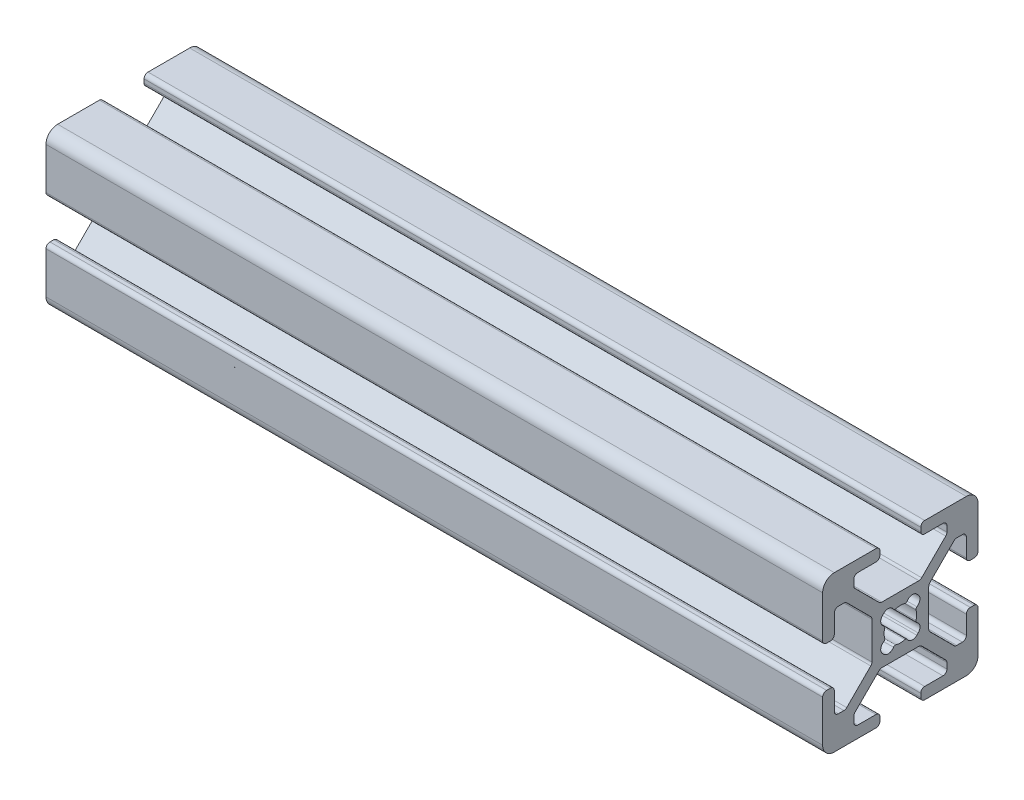
SolidWorks part; units mm, degrees
ref_plane "Front Plane" through (0, 0, 0) normal (0, 0, 1) x (1, 0, 0)
ref_plane "Top Plane" through (0, 0, 0) normal (0, 1, 0) x (1, 0, 0)
ref_plane "Right Plane" through (0, 0, 0) normal (1, 0, 0) x (0, 0, -1)
sketch "Sketch1" plane through (0, 0, 0) normal (0, 0, 1) x (1, 0, 0)
  line L0 (0, 0) -> (100, 0)
  dimension "D1" = 100
other "20_series 20-2020(1)"
ref_plane "Plane1" through (0, 0, 0) normal (1, 0, 0) x (0, 1, 0)
sketch "Sketch11" plane through (0, 0, 0) normal (1, 0, 0) x (0, 1, 0)
  line L0 (9.0094, 2.6289) -> (9.492, 2.6289)
  line L1 (8.5014, 5.4864) -> (8.5014, 3.1369)
  line L2 (10, 8.5014) -> (10, 3.1369)
  line L3 (7.2645, 5.9944) -> (7.9934, 5.9944)
  line L4 (3.1369, 10) -> (8.5014, 10)
  line L5 (3.8074, 2.7477) -> (6.9053, 5.8456)
  line L6 (2.6289, 9.0094) -> (2.6289, 9.492)
  line L7 (3.6586, -2.3885) -> (3.6586, 2.3885)
  line L8 (3.1369, 8.5014) -> (5.4864, 8.5014)
  line L9 (6.9053, -5.8456) -> (3.8074, -2.7477)
  line L10 (5.9944, 7.9934) -> (5.9944, 7.2645)
  line L11 (7.9934, -5.9944) -> (7.2645, -5.9944)
  line L12 (5.8456, 6.9053) -> (2.7477, 3.8074)
  line L13 (8.5014, -3.1369) -> (8.5014, -5.4864)
  line L14 (2.3885, 3.6586) -> (-2.3885, 3.6586)
  line L15 (9.0094, -2.6289) -> (9.492, -2.6289)
  line L16 (-2.7477, 3.8074) -> (-5.8456, 6.9053)
  line L17 (10, -3.1369) -> (10, -8.5014)
  line L18 (-5.9944, 7.2645) -> (-5.9944, 7.9934)
  line L19 (8.5014, -10) -> (3.1369, -10)
  line L20 (-5.4864, 8.5014) -> (-3.1369, 8.5014)
  line L21 (2.6289, -9.0094) -> (2.6289, -9.492)
  line L22 (-2.6289, 9.0094) -> (-2.6289, 9.492)
  line L23 (5.4864, -8.5014) -> (3.1369, -8.5014)
  line L24 (-8.5014, 10) -> (-3.1369, 10)
  line L25 (5.9944, -7.2645) -> (5.9944, -7.9934)
  line L26 (-10, 3.1369) -> (-10, 8.5014)
  line L27 (2.7477, -3.8074) -> (5.8456, -6.9053)
  line L28 (-9.0094, 2.6289) -> (-9.492, 2.6289)
  line L29 (-2.3885, -3.6586) -> (2.3885, -3.6586)
  line L30 (-8.5014, 3.1369) -> (-8.5014, 5.4864)
  line L31 (-5.8456, -6.9053) -> (-2.7477, -3.8074)
  line L32 (-7.9934, 5.9944) -> (-7.2645, 5.9944)
  line L33 (-5.9944, -7.9934) -> (-5.9944, -7.2645)
  line L34 (-6.9053, 5.8456) -> (-3.8074, 2.7477)
  line L35 (-3.1369, -8.5014) -> (-5.4864, -8.5014)
  line L36 (-3.6586, 2.3885) -> (-3.6586, -2.3885)
  line L37 (-2.6289, -9.0094) -> (-2.6289, -9.492)
  line L38 (-3.8074, -2.7477) -> (-6.9053, -5.8456)
  line L39 (-3.1369, -10) -> (-8.5014, -10)
  line L40 (-7.2645, -5.9944) -> (-7.9934, -5.9944)
  line L41 (-10, -8.5014) -> (-10, -3.1369)
  line L42 (-8.5014, -5.4864) -> (-8.5014, -3.1369)
  line L43 (-9.0094, -2.6289) -> (-9.492, -2.6289)
  line L44 (-2.2966, 2.1217) -> (-2.1217, 2.2966)
  line L45 (2.1217, 2.2966) -> (2.2966, 2.1217)
  line L46 (-2.1217, -2.2966) -> (-2.2966, -2.1217)
  line L47 (2.2966, -2.1217) -> (2.1217, -2.2966)
  arc A0 (8.5014, 3.1369) -> (9.0094, 2.6289) centre (9.0094, 3.1369) ccw
  arc A1 (9.492, 2.6289) -> (10, 3.1369) centre (9.492, 3.1369) ccw
  arc A2 (8.5014, 5.4864) -> (7.9934, 5.9944) centre (7.9934, 5.4864) ccw
  arc A3 (10, 8.5014) -> (8.5014, 10) centre (8.5014, 8.5014) ccw
  arc A4 (7.2645, 5.9944) -> (6.9053, 5.8456) centre (7.2645, 5.4864) ccw
  arc A5 (3.1369, 10) -> (2.6289, 9.492) centre (3.1369, 9.492) ccw
  arc A6 (3.8074, 2.7477) -> (3.6586, 2.3885) centre (4.1666, 2.3885) ccw
  arc A7 (2.6289, 9.0094) -> (3.1369, 8.5014) centre (3.1369, 9.0094) ccw
  arc A8 (3.6586, -2.3885) -> (3.8074, -2.7477) centre (4.1666, -2.3885) ccw
  arc A9 (5.9944, 7.9934) -> (5.4864, 8.5014) centre (5.4864, 7.9934) ccw
  arc A10 (6.9053, -5.8456) -> (7.2645, -5.9944) centre (7.2645, -5.4864) ccw
  arc A11 (5.8456, 6.9053) -> (5.9944, 7.2645) centre (5.4864, 7.2645) ccw
  arc A12 (7.9934, -5.9944) -> (8.5014, -5.4864) centre (7.9934, -5.4864) ccw
  arc A13 (2.3885, 3.6586) -> (2.7477, 3.8074) centre (2.3885, 4.1666) ccw
  arc A14 (9.0094, -2.6289) -> (8.5014, -3.1369) centre (9.0094, -3.1369) ccw
  arc A15 (-2.7477, 3.8074) -> (-2.3885, 3.6586) centre (-2.3885, 4.1666) ccw
  arc A16 (10, -3.1369) -> (9.492, -2.6289) centre (9.492, -3.1369) ccw
  arc A17 (-5.9944, 7.2645) -> (-5.8456, 6.9053) centre (-5.4864, 7.2645) ccw
  arc A18 (8.5014, -10) -> (10, -8.5014) centre (8.5014, -8.5014) ccw
  arc A19 (-5.4864, 8.5014) -> (-5.9944, 7.9934) centre (-5.4864, 7.9934) ccw
  arc A20 (2.6289, -9.492) -> (3.1369, -10) centre (3.1369, -9.492) ccw
  arc A21 (-3.1369, 8.5014) -> (-2.6289, 9.0094) centre (-3.1369, 9.0094) ccw
  arc A22 (3.1369, -8.5014) -> (2.6289, -9.0094) centre (3.1369, -9.0094) ccw
  arc A23 (-2.6289, 9.492) -> (-3.1369, 10) centre (-3.1369, 9.492) ccw
  arc A24 (5.4864, -8.5014) -> (5.9944, -7.9934) centre (5.4864, -7.9934) ccw
  arc A25 (-8.5014, 10) -> (-10, 8.5014) centre (-8.5014, 8.5014) ccw
  arc A26 (5.9944, -7.2645) -> (5.8456, -6.9053) centre (5.4864, -7.2645) ccw
  arc A27 (-10, 3.1369) -> (-9.492, 2.6289) centre (-9.492, 3.1369) ccw
  arc A28 (2.7477, -3.8074) -> (2.3885, -3.6586) centre (2.3885, -4.1666) ccw
  arc A29 (-9.0094, 2.6289) -> (-8.5014, 3.1369) centre (-9.0094, 3.1369) ccw
  arc A30 (-2.3885, -3.6586) -> (-2.7477, -3.8074) centre (-2.3885, -4.1666) ccw
  arc A31 (-7.9934, 5.9944) -> (-8.5014, 5.4864) centre (-7.9934, 5.4864) ccw
  arc A32 (-5.8456, -6.9053) -> (-5.9944, -7.2645) centre (-5.4864, -7.2645) ccw
  arc A33 (-6.9053, 5.8456) -> (-7.2645, 5.9944) centre (-7.2645, 5.4864) ccw
  arc A34 (-5.9944, -7.9934) -> (-5.4864, -8.5014) centre (-5.4864, -7.9934) ccw
  arc A35 (-3.6586, 2.3885) -> (-3.8074, 2.7477) centre (-4.1666, 2.3885) ccw
  arc A36 (-2.6289, -9.0094) -> (-3.1369, -8.5014) centre (-3.1369, -9.0094) ccw
  arc A37 (-3.8074, -2.7477) -> (-3.6586, -2.3885) centre (-4.1666, -2.3885) ccw
  arc A38 (-3.1369, -10) -> (-2.6289, -9.492) centre (-3.1369, -9.492) ccw
  arc A39 (-7.2645, -5.9944) -> (-6.9053, -5.8456) centre (-7.2645, -5.4864) ccw
  arc A40 (-10, -8.5014) -> (-8.5014, -10) centre (-8.5014, -8.5014) ccw
  arc A41 (-8.5014, -5.4864) -> (-7.9934, -5.9944) centre (-7.9934, -5.4864) ccw
  arc A42 (-9.492, -2.6289) -> (-10, -3.1369) centre (-9.492, -3.1369) ccw
  arc A43 (-8.5014, -3.1369) -> (-9.0094, -2.6289) centre (-9.0094, -3.1369) ccw
  arc A44 (-0.8806, 2.1293) -> (-0.5885, 2.0112) centre (-0.6599, 2.2549) ccw
  arc A45 (0.5885, 2.0112) -> (-0.5885, 2.0112) centre (0, 0) ccw
  arc A46 (-0.8806, 2.1293) -> (-2.1217, 2.2966) centre (-1.565, 1.7398) ccw
  arc A47 (0.5885, 2.0112) -> (0.8806, 2.1293) centre (0.6599, 2.2549) ccw
  arc A48 (2.1217, 2.2966) -> (0.8806, 2.1293) centre (1.565, 1.7398) ccw
  arc A49 (-2.2966, 2.1217) -> (-2.1293, 0.8806) centre (-1.7398, 1.565) ccw
  arc A50 (-2.0112, 0.5885) -> (-2.1293, 0.8806) centre (-2.2549, 0.6599) ccw
  arc A51 (2.1293, 0.8806) -> (2.2966, 2.1217) centre (1.7398, 1.565) ccw
  arc A52 (-2.0112, 0.5885) -> (-2.0112, -0.5885) centre (0, 0) ccw
  arc A53 (2.1293, 0.8806) -> (2.0112, 0.5885) centre (2.2549, 0.6599) ccw
  arc A54 (-2.1293, -0.8806) -> (-2.0112, -0.5885) centre (-2.2549, -0.6599) ccw
  arc A55 (2.0112, -0.5885) -> (2.0112, 0.5885) centre (0, 0) ccw
  arc A56 (-2.1293, -0.8806) -> (-2.2966, -2.1217) centre (-1.7398, -1.565) ccw
  arc A57 (2.0112, -0.5885) -> (2.1293, -0.8806) centre (2.2549, -0.6599) ccw
  arc A58 (2.2966, -2.1217) -> (2.1293, -0.8806) centre (1.7398, -1.565) ccw
  arc A59 (-2.1217, -2.2966) -> (-0.8806, -2.1293) centre (-1.565, -1.7398) ccw
  arc A60 (-0.5885, -2.0112) -> (-0.8806, -2.1293) centre (-0.6599, -2.2549) ccw
  arc A61 (0.8806, -2.1293) -> (2.1217, -2.2966) centre (1.565, -1.7398) ccw
  arc A62 (-0.5885, -2.0112) -> (0.5885, -2.0112) centre (0, 0) ccw
  arc A63 (0.8806, -2.1293) -> (0.5885, -2.0112) centre (0.6599, -2.2549) ccw
  point P0 (0, 0)
